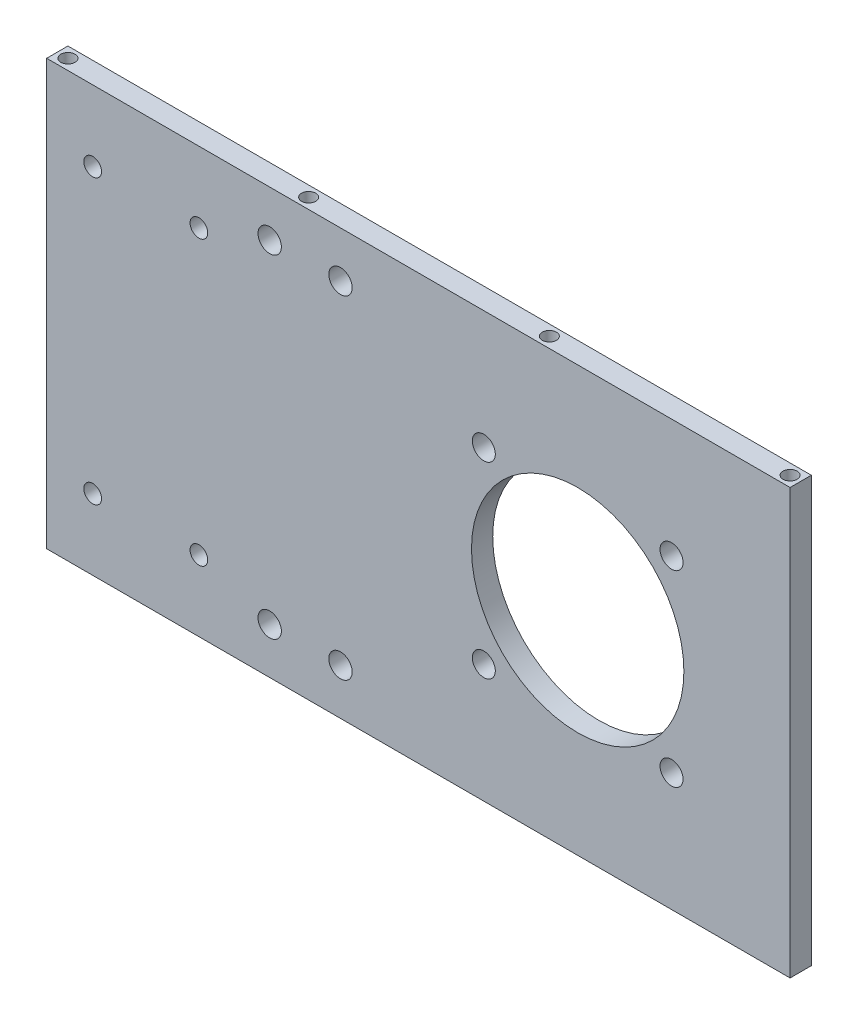
SolidWorks part; units mm, degrees
material "6061 合金"
ref_plane "前视基准面" through (0, 0, 0) normal (0, 0, 1) x (1, 0, 0)
ref_plane "上视基准面" through (0, 0, 0) normal (0, 1, 0) x (1, 0, 0)
ref_plane "右视基准面" through (0, 0, 0) normal (1, 0, 0) x (0, 0, -1)
sketch "草图1" plane through (0, 0, 0) normal (0, 0, 1) x (1, 0, 0)
  line L0 (0, 0) -> (26.5165, 26.5165) construction
  line L1 (0, 0) -> (91.6131, 0) construction
  line L2 (60, -60) -> (60, 60)
  line L3 (60, 60) -> (-150, 60)
  line L4 (-150, 60) -> (-150, -60)
  line L5 (60, -60) -> (-150, -60)
  circle A0 centre (26.5165, 26.5165) radius 3.25
  circle A1 centre (26.5165, -26.5165) radius 3.25
  circle A2 centre (-26.5165, -26.5165) radius 3.25
  circle A3 centre (-26.5165, 26.5165) radius 3.25
  circle A4 centre (0, 0) radius 30
  point P14 (0, 0)
  point P18 (60, 0)
  point P19 (-150, 0)
  dimension "D1" = 45
  dimension "D3" = 6.5
  dimension "D5" = 60
  dimension "D8" = 60
  dimension "D2" = 37.5
  dimension "D6" = 120
  dimension "D7" = 150
  dimension "D4" = 4
extrude "凸台-拉伸1" add sketch "草图1" along normal blind 6
sketch "草图2" plane through (0, 0, 6) normal (0, 0, 1) x (1, 0, 0)
  line L0 (60, 60) -> (-150, 60) construction
  line L1 (-150, 60) -> (-150, -60) construction
  line L2 (-107, 40) -> (-107, -40) construction
  line L3 (-107, -40) -> (-137, -40) construction
  line L4 (-137, -40) -> (-137, 40) construction
  line L5 (-137, 40) -> (-107, 40) construction
  circle A0 centre (-137, 40) radius 2.5
  circle A1 centre (-107, 40) radius 2.5
  circle A2 centre (-107, -40) radius 2.5
  circle A3 centre (-137, -40) radius 2.5
  dimension "D1" = 5
  dimension "D2" = 20
  dimension "D3" = 13
  dimension "D4" = 2
  dimension "D5" = 2
extrude "切除-拉伸1" cut sketch "草图2" against normal blind 10
sketch "草图3" plane through (0, -60, 0) normal (0, -1, 0) x (-1, 0, 0)
  line L0 (150, 0) -> (-60, 0) construction
  line L1 (-60, -6) -> (-60, 0) construction
  circle A0 centre (-57, -3) radius 2
  circle A1 centre (11, -3) radius 2
  circle A2 centre (79, -3) radius 2
  circle A3 centre (147, -3) radius 2
  dimension "D1" = 3
  dimension "D2" = 3
  dimension "D3" = 4
extrude "切除-拉伸2" cut sketch "草图3" against normal blind 20
ref_plane "基准面1" through (0, 0, 0) normal (0, -1, 0) x (-1, 0, 0)
mirror "镜向3" about plane through (0, 0, 0) normal (0, -1, 0) of "切除-拉伸2"
sketch "草图4" plane through (0, 0, 6) normal (0, 0, 1) x (1, 0, 0)
  line L0 (-77, 60) -> (-77, 2.6993) construction
  line L1 (60, 60) -> (-150, 60) construction
  line L2 (-150, 60) -> (-150, -60) construction
  line L3 (-150, 0) -> (0, 0) construction
  circle A0 centre (-87, 47) radius 3.3
  circle A1 centre (-67, 47) radius 3.3
  circle A2 centre (-67, -47) radius 3.3
  circle A3 centre (-87, -47) radius 3.3
  dimension "D2" = 6.6
  dimension "D3" = 10
  dimension "D4" = 13
  dimension "D1" = 73
extrude "切除-拉伸3" cut sketch "草图4" against normal blind 10
